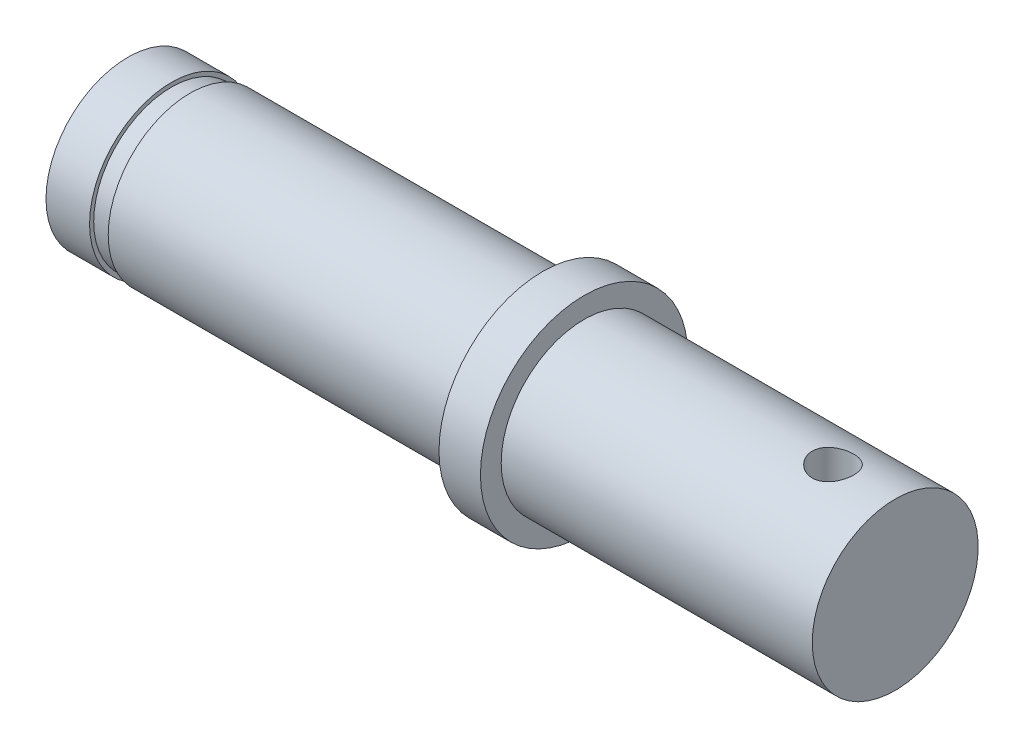
SolidWorks part; units mm, degrees
material "6061 合金"
ref_plane "前视基准面" through (0, 0, 0) normal (0, 0, 1) x (1, 0, 0)
ref_plane "上视基准面" through (0, 0, 0) normal (0, 1, 0) x (1, 0, 0)
ref_plane "右视基准面" through (0, 0, 0) normal (1, 0, 0) x (0, 0, -1)
sketch "草图1" plane through (0, 0, 0) normal (0, 0, 1) x (1, 0, 0)
  line L0 (-15.4994, 0) -> (21.5006, 0)
  line L1 (21.5006, 0) -> (21.5006, 4)
  line L2 (21.5006, 4) -> (6.5006, 4)
  line L3 (6.5006, 4) -> (6.5006, 5)
  line L4 (6.5006, 5) -> (4.5006, 5)
  line L5 (4.5006, 5) -> (4.5006, 3.95)
  line L6 (4.5006, 3.95) -> (-12.4994, 3.95)
  line L7 (-15.4994, 3.95) -> (-15.4994, 0)
  line L8 (-13.3994, 3.95) -> (-13.3994, 3.75)
  line L9 (-13.3994, 3.75) -> (-12.4994, 3.75)
  line L10 (-12.4994, 3.75) -> (-12.4994, 3.95)
  line L11 (-13.3994, 3.95) -> (-15.4994, 3.95)
  dimension "D1" = 0.9
  dimension "D2" = 0.2
  dimension "D3" = 3.95
  dimension "D4" = 5
  dimension "D5" = 15
  dimension "D6" = 2
  dimension "D7" = 20
  dimension "D8" = 17
  dimension "D9" = 4
revolve "旋转1" add sketch "草图1" angle 360 about L0
sketch "草图2" plane through (0, 0, 0) normal (0, 1, 0) x (1, 0, 0)
  line L0 (-21.8469, 0) -> (35.0006, 0) construction
  line L1 (6.5006, -5) -> (6.5006, 5) construction
  circle A0 centre (18.5006, 0) radius 1
  dimension "D1" = 2
  dimension "D2" = 12
extrude "切除-拉伸1" cut sketch "草图2" against normal mid plane 10
